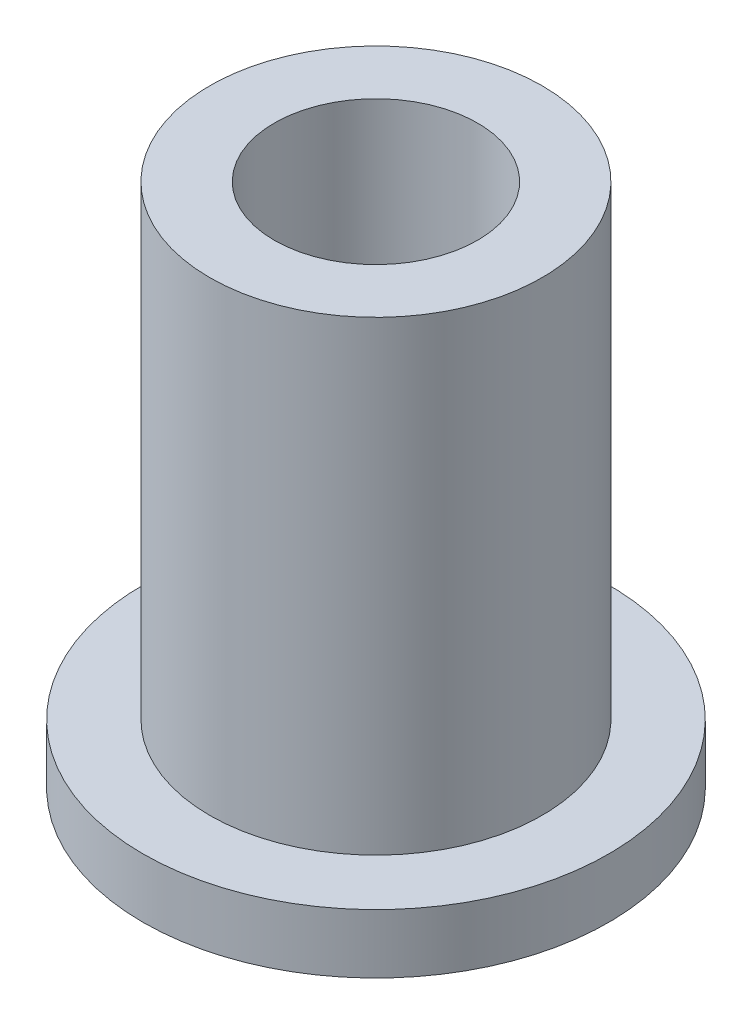
SolidWorks part; units mm, degrees
material "Commercial Bronze, UNS C22000 (90-10 Bronze)"
ref_plane "Front Plane" through (0, 0, 0) normal (0, 0, 1) x (1, 0, 0)
ref_plane "Top Plane" through (0, 0, 0) normal (0, 1, 0) x (1, 0, 0)
ref_plane "Right Plane" through (0, 0, 0) normal (1, 0, 0) x (0, 0, -1)
ref_plane "Plane1" through (0, 0, 0) normal (0, 0, -1) x (-1, 0, 0)
sketch "Sketch1" plane through (0, 0, 0) normal (0, 0, -1) x (-1, 0, 0)
  line L0 (-5.5, 0) -> (-2.6, 0)
  line L1 (-2.6, 0) -> (-2.4, 0.2)
  line L2 (-2.4, 0.2) -> (-2.4, 12.4)
  line L3 (-2.4, 12.4) -> (-3.925, 12.4)
  line L4 (-3.925, 12.4) -> (-3.925, 1.4)
  line L5 (-3.925, 1.4) -> (-5.5, 1.4)
  line L6 (-5.5, 1.4) -> (-5.5, 0)
  line L7 (0, 0) -> (0, 12.4) construction
revolve "Revolve1" add sketch "Sketch1" angle 360 about L7
